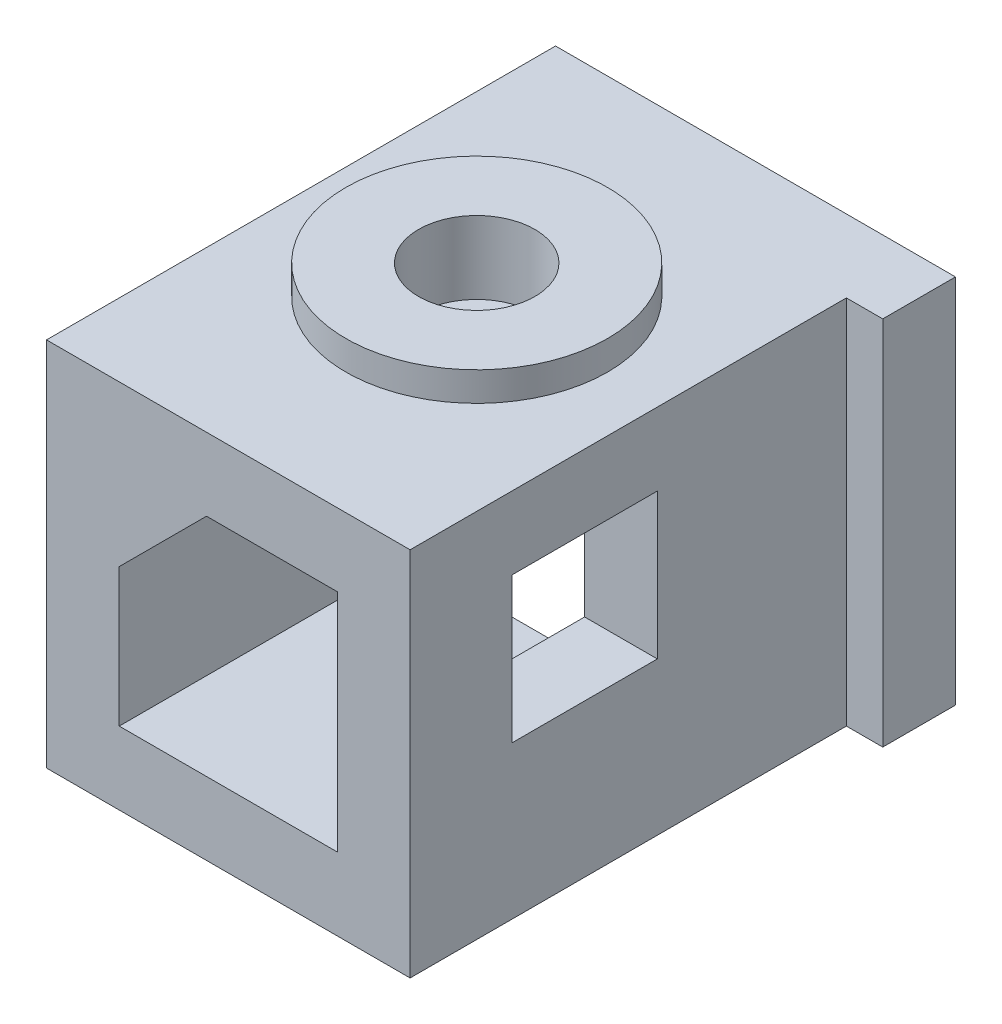
SolidWorks part; units mm, degrees
ref_plane "Front Plane" through (0, 0, 0) normal (0, 0, 1) x (1, 0, 0)
ref_plane "Top Plane" through (0, 0, 0) normal (0, 1, 0) x (1, 0, 0)
ref_plane "Right Plane" through (0, 0, 0) normal (1, 0, 0) x (0, 0, -1)
sketch "Sketch1" plane through (0, 0, 0) normal (0, 0, 1) x (1, 0, 0)
  line L0 (-9.3056, 4.7356) -> (15.6944, 4.7356)
  line L1 (15.6944, 4.7356) -> (15.6944, -0.2644)
  line L2 (15.6944, -0.2644) -> (1.6944, -0.2644)
  line L3 (1.6944, -0.2644) -> (-4.3056, -6.2644)
  line L4 (-4.3056, -6.2644) -> (-4.3056, -13.2644)
  line L5 (-4.3056, -13.2644) -> (-9.3056, -13.2644)
  line L6 (-9.3056, -13.2644) -> (-9.3056, 4.7356)
  line L7 (-4.3056, -6.2644) -> (-4.3056, -0.2644) construction
  line L8 (-4.3056, -0.2644) -> (1.6944, -0.2644) construction
  dimension "D1" = 18
  dimension "D2" = 25
  dimension "D3" = 5
  dimension "D4" = 5
  dimension "D5" = 6
  dimension "D6" = 6
extrude "Boss-Extrude1" add sketch "Sketch1" along normal blind 35
sketch "Sketch2" plane through (0, 4.7356, 0) normal (0, 1, 0) x (1, 0, 0)
  line L0 (-9.3056, -35) -> (-9.3056, 0) construction
  line L1 (15.6944, 0) -> (-9.3056, 0) construction
  circle A0 centre (2.9044, -17.63) radius 9
  dimension "D1" = 18
  dimension "D2" = 12.21
  dimension "D3" = 17.63
extrude "Boss-Extrude2" add sketch "Sketch2" along normal blind 2
sketch "Sketch3" plane through (0, 6.7356, 0) normal (0, 1, 0) x (1, 0, 0)
  circle A0 centre (2.9044, -17.63) radius 4
  dimension "D1" = 8
extrude "Cut-Extrude1" cut sketch "Sketch3" against normal blind 5
sketch "Sketch4" plane through (0, -0.2644, 0) normal (0, -1, 0) x (1, 0, 0)
  line L0 (1.6944, 35) -> (15.6944, 35) construction
  line L1 (15.6944, 35) -> (10.6944, 35)
  line L2 (15.6944, 35) -> (15.6944, 0)
  line L3 (15.6944, 0) -> (10.6944, 0)
  line L4 (10.6944, 35) -> (10.6944, 0)
  line L5 (15.6944, 35) -> (15.6944, 0) construction
  line L6 (1.6944, 0) -> (15.6944, 0) construction
  dimension "D1" = 5
extrude "Boss-Extrude3" add sketch "Sketch4" along normal blind 20.5
sketch "Sketch6" plane through (15.6944, 0, 0) normal (1, 0, 0) x (0, 0, -1)
  line L0 (-35, 4.7356) -> (0, 4.7356) construction
  line L1 (0, -20.7644) -> (-5, -20.7644)
  line L2 (0, -20.7644) -> (0, 4.7356)
  line L3 (0, 4.7356) -> (-5, 4.7356)
  line L4 (-5, -20.7644) -> (-5, 4.7356)
  dimension "D1" = 5
extrude "Boss-Extrude4" add sketch "Sketch6" along normal blind 2.5
sketch "Sketch7" plane through (0, -13.2644, 0) normal (0, -1, 0) x (1, 0, 0)
  line L0 (-4.3056, 35) -> (-4.3056, 0) construction
  line L1 (-9.3056, 35) -> (-4.3056, 35)
  line L2 (-9.3056, 35) -> (-9.3056, 15)
  line L3 (-9.3056, 15) -> (-4.3056, 15)
  line L4 (-4.3056, 35) -> (-4.3056, 15)
  dimension "D1" = 20
extrude "Boss-Extrude5" add sketch "Sketch7" along normal up to surface (7.5 mm away) up to face at (14.8611, -20.7644, 13.3333)
sketch "Sketch8" plane through (-4.3056, 0, 0) normal (1, 0, 0) x (0, 0, -1)
  line L0 (-15, -20.7644) -> (-15, -13.2644) construction
  line L1 (-35, -20.7644) -> (-15, -20.7644)
  line L2 (-35, -20.7644) -> (-35, -15.7644)
  line L3 (-35, -15.7644) -> (-15, -15.7644)
  line L4 (-15, -20.7644) -> (-15, -15.7644)
  dimension "D1" = 5
extrude "Boss-Extrude6" add sketch "Sketch8" along normal up to surface (15 mm away) up to face at (10.6944, -10.5144, 17.5)
sketch "Sketch10" plane through (15.6944, 0, 0) normal (1, 0, 0) x (0, 0, -1)
  line L0 (-35, 4.7356) -> (-5, 4.7356) construction
  line L1 (-28, -0.2644) -> (-18, -0.2644)
  line L2 (-28, -0.2644) -> (-28, -10.2644)
  line L3 (-28, -10.2644) -> (-18, -10.2644)
  line L4 (-18, -0.2644) -> (-18, -10.2644)
  line L5 (-28, -0.2644) -> (-18, -10.2644) construction
  line L6 (-28, -10.2644) -> (-18, -0.2644) construction
  line L7 (-35, -20.7644) -> (-35, 4.7356) construction
  point P0 (-23, -5.2644)
  dimension "D1" = 10
  dimension "D2" = 10
  dimension "D3" = 10
  dimension "D4" = 12
extrude "Cut-Extrude2" cut sketch "Sketch10" against normal up to surface (5 mm away) up to face at (10.6944, -12.2644, 16.6667)
